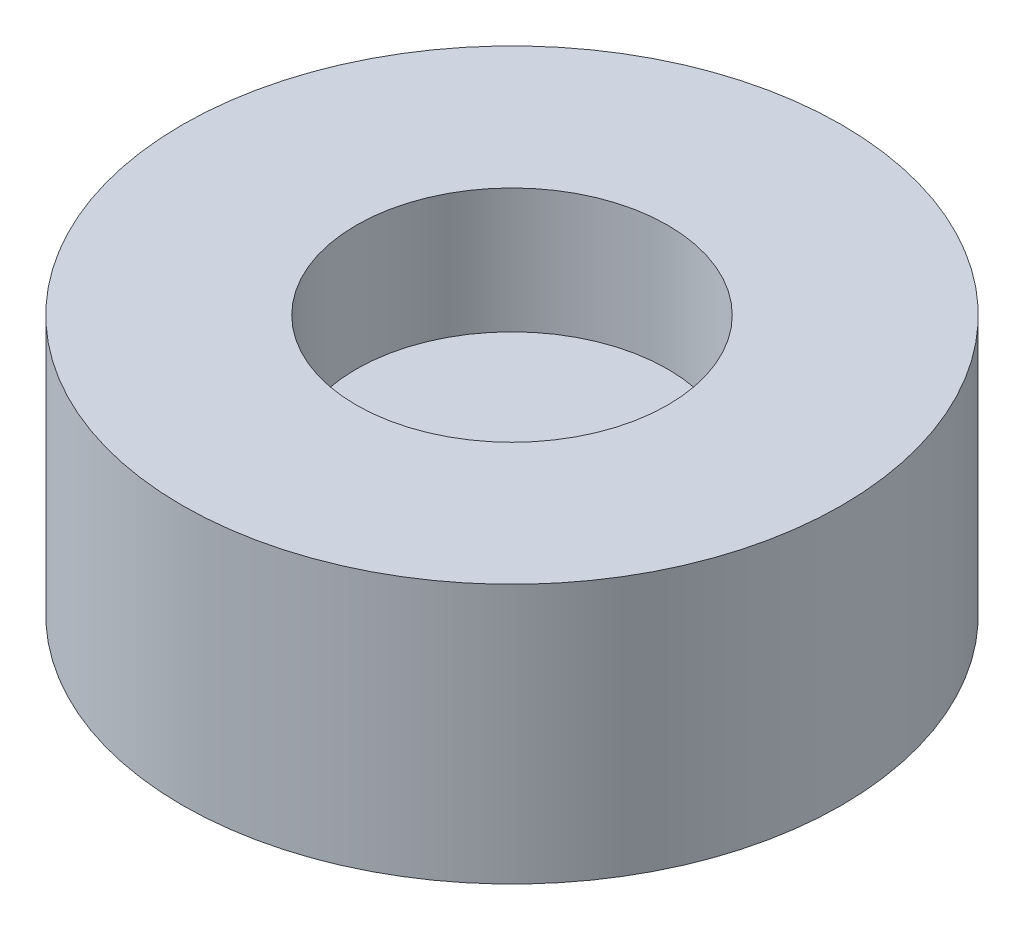
SolidWorks part; units mm, degrees
ref_plane "前视基准面" through (0, 0, 0) normal (0, 0, 1) x (1, 0, 0)
ref_plane "上视基准面" through (0, 0, 0) normal (0, 1, 0) x (1, 0, 0)
ref_plane "右视基准面" through (0, 0, 0) normal (1, 0, 0) x (0, 0, -1)
other "Configuration Table"
sketch "Sketch1" plane through (0, 0, 0) normal (0, 1, 0) x (1, 0, 0)
  circle A0 centre (0, 0) radius 6.35
  dimension "D1" = 12.7
extrude "Boss-Extrude1" add sketch "Sketch1" along normal blind 5
sketch "Sketch2" plane through (0, 5, 0) normal (0, 1, 0) x (1, 0, 0)
  circle A0 centre (0, 0) radius 3
  dimension "D1" = 6
extrude "Cut-Extrude1" cut sketch "Sketch2" against normal blind 2.4
